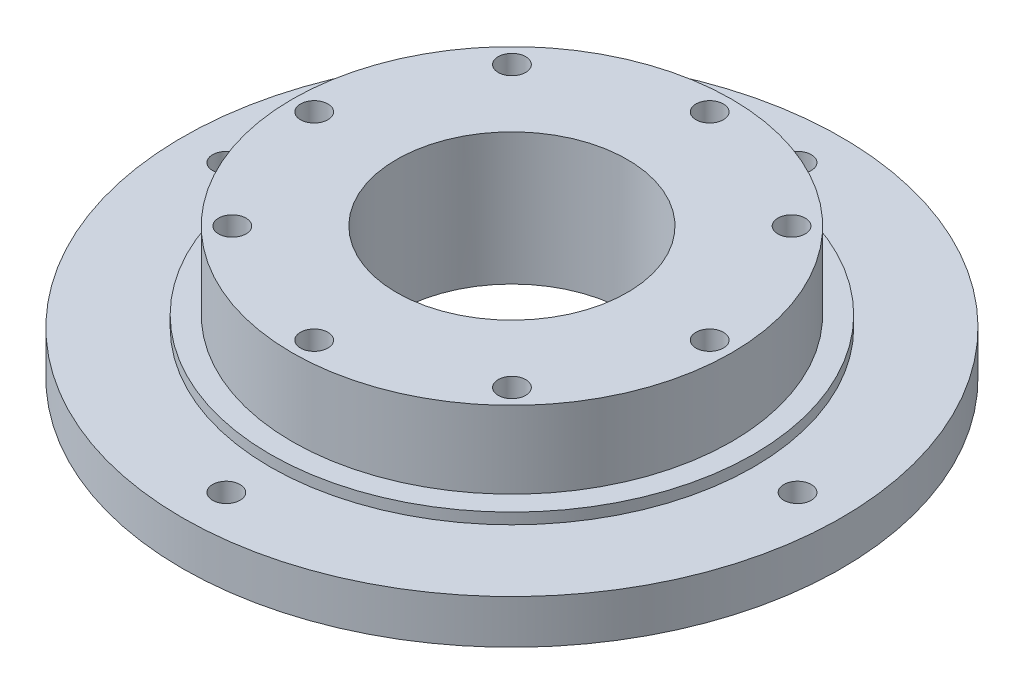
SolidWorks part; units mm, degrees
material "cus-Plastic-PLA-pro"
ref_plane "Front Plane" through (0, 0, 0) normal (0, 0, 1) x (1, 0, 0)
ref_plane "Top Plane" through (0, 0, 0) normal (0, 1, 0) x (1, 0, 0)
ref_plane "Right Plane" through (0, 0, 0) normal (1, 0, 0) x (0, 0, -1)
sketch "Sketch1" plane through (0, 0, 0) normal (0, 1, 0) x (1, 0, 0)
  circle A0 centre (0, 0) radius 30
extrude "base-core" add sketch "Sketch1" against normal blind 4
sketch "Sketch2" plane through (0, 0, 0) normal (0, 1, 0) x (1, 0, 0)
  circle A0 centre (0, 0) radius 22
extrude "clearness" add sketch "Sketch2" along normal blind 1
sketch "Sketch3" plane through (0, 1, 0) normal (0, 1, 0) x (1, 0, 0)
  circle A0 centre (0, 0) radius 20
extrude "breaing-40-ID" add sketch "Sketch3" along normal blind 7
sketch "Sketch4" plane through (0, 8, 0) normal (0, 1, 0) x (1, 0, 0)
  circle A0 centre (0, 0) radius 10.5
extrude "breaing-21-OD" cut sketch "Sketch4" against normal blind 5
sketch "Sketch5" plane through (0, -4, 0) normal (0, -1, 0) x (1, 0, 0)
  circle A0 centre (0, 0) radius 10.5
  dimension "D1" = 21
extrude "motor-cut" cut sketch "Sketch5" against normal up to surface (7 mm away) up to face at (0, 3, 10.5)
sketch "Sketch10" plane through (0, 8, 0) normal (0, 1, 0) x (1, 0, 0)
  circle A0 centre (0, 0) radius 18 construction
  point P3 (18, 0)
  point P7 (12.7279, -12.7279)
  point P8 (0, -18)
  point P9 (-12.7279, -12.7279)
  point P10 (-18, 0)
  point P11 (-12.7279, 12.7279)
  point P12 (0, 18)
  point P13 (12.7279, 12.7279)
  point P14 (0, 0)
  dimension "D1" = 8
  dimension "D2" = 18
hole_wizard "M3 Tapped Hole2" positions "Sketch10" profile "Sketch11" tap size "M3" standard "ISO"
sketch "Sketch11" plane through (12.7279, 8, -12.7279) normal (1, 0, 0) x (0, 0, 1)
  line L0 (0, 0) -> (0, 7.5)
  line L1 (0, 7.5) -> (1.25, 6.7489)
  line L2 (1.25, 6.7489) -> (1.25, 0)
  line L5 (1.25, 0) -> (0, 0)
  line L10 (0, 7.5) -> (-1.25, 6.7489) construction
  line L11 (0, -6.35) -> (0, 107.95) construction
  dimension "Tap Drill Dia." = 2.5
  dimension "Tap Drill Depth" = 7.5
  dimension "Drill Angle" = 118
sketch "Sketch12" plane through (0, -4, 0) normal (0, -1, 0) x (1, 0, 0)
  circle A0 centre (0, 0) radius 26 construction
  point P38 (0, 26)
  point P66 (26, 0)
  point P67 (0, -26)
  point P68 (-26, 0)
  dimension "D1" = 26
  dimension "D2" = 4
hole_wizard "M3 Tapped Hole1" positions "Sketch12" profile "Sketch13" tap size "M3" standard "ISO" end condition through all
sketch "Sketch13" plane through (-26, -4, 0) normal (1, 0, 0) x (0, 0, -1)
  line L0 (0, 0) -> (0, 12)
  line L1 (0, 12) -> (1.25, 12)
  line L2 (1.25, 12) -> (1.25, 0)
  line L5 (1.25, 0) -> (0, 0)
  line L11 (0, -6.35) -> (0, 107.95) construction
  dimension "Thru Tap Drill Dia." = 2.5
  dimension "Thru Tap Drill Depth" = 12
cosmetic thread "Hole Thread1" parameters "D2"=3
cosmetic thread "Hole Thread9" parameters "D2"=3
cosmetic thread "Hole Thread10" parameters "D2"=3
cosmetic thread "Hole Thread11" parameters "D2"=3
